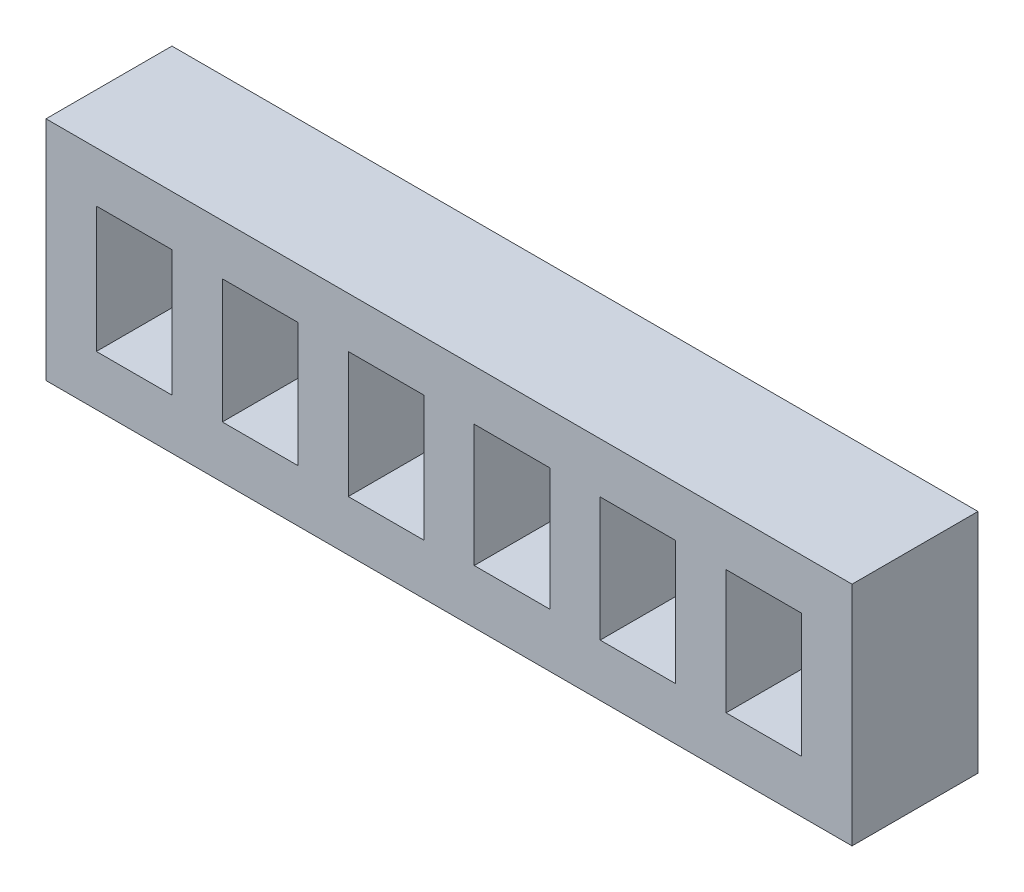
SolidWorks part; units mm, degrees
ref_plane "Front Plane" through (0, 0, 0) normal (0, 0, 1) x (1, 0, 0)
ref_plane "Top Plane" through (0, 0, 0) normal (0, 1, 0) x (1, 0, 0)
ref_plane "Right Plane" through (0, 0, 0) normal (1, 0, 0) x (0, 0, -1)
sketch "Sketch3" plane through (0, 0, 0) normal (0, 0, 1) x (1, 0, 0)
  line L0 (-26.4518, 9.6505) -> (-23.4518, 9.6505)
  line L9 (-33.4518, 11.6505) -> (-1.4518, 11.6505)
  line L10 (-33.4518, 11.6505) -> (-33.4518, 2.6505)
  line L11 (-33.4518, 2.6505) -> (-1.4518, 2.6505)
  line L12 (-1.4518, 11.6505) -> (-1.4518, 2.6505)
  line L13 (-31.4518, 9.6505) -> (-28.4518, 9.6505)
  line L14 (-31.4518, 9.6505) -> (-31.4518, 4.6505)
  line L15 (-31.4518, 4.6505) -> (-28.4518, 4.6505)
  line L16 (-28.4518, 9.6505) -> (-28.4518, 4.6505)
  line L17 (-26.4518, 9.6505) -> (-26.4518, 4.7268)
  line L18 (-26.4518, 4.7268) -> (-23.4518, 4.7268)
  line L19 (-23.4518, 9.6505) -> (-23.4518, 4.7268)
  line L20 (-21.4518, 9.6505) -> (-18.4518, 9.6505)
  line L21 (-21.4518, 9.6505) -> (-21.4518, 4.663)
  line L22 (-21.4518, 4.663) -> (-18.4518, 4.663)
  line L23 (-18.4518, 9.6505) -> (-18.4518, 4.663)
  line L24 (-16.4518, 9.6505) -> (-13.4518, 9.6505)
  line L25 (-16.4518, 9.6505) -> (-16.4518, 4.7906)
  line L26 (-16.4518, 4.7906) -> (-13.4518, 4.7906)
  line L27 (-13.4518, 9.6505) -> (-13.4518, 4.7906)
  line L28 (-11.4518, 9.6505) -> (-8.4518, 9.6505)
  line L29 (-11.4518, 9.6505) -> (-11.4518, 4.7268)
  line L30 (-11.4518, 4.7268) -> (-8.4518, 4.7268)
  line L31 (-8.4518, 9.6505) -> (-8.4518, 4.7268)
  line L32 (-6.4518, 9.6505) -> (-3.4518, 9.6505)
  line L33 (-6.4518, 9.6505) -> (-6.4518, 4.7268)
  line L34 (-6.4518, 4.7268) -> (-3.4518, 4.7268)
  line L35 (-3.4518, 9.6505) -> (-3.4518, 4.7268)
  point P28 (-24.9518, 9.6505)
  dimension "D1" = 9
  dimension "D2" = 32
  dimension "D3" = 2
  dimension "D4" = 2
  dimension "D5" = 2
  dimension "D6" = 3
  dimension "D7" = 2
  dimension "D8" = 2
  dimension "D9" = 2
  dimension "D10" = 2
  dimension "D11" = 2
  dimension "D12" = 2
  dimension "D13" = 2
  dimension "D14" = 2
  dimension "D15" = 2
  dimension "D16" = 2
  dimension "D17" = 2
extrude "Boss-Extrude1" add sketch "Sketch3" along normal blind 5
